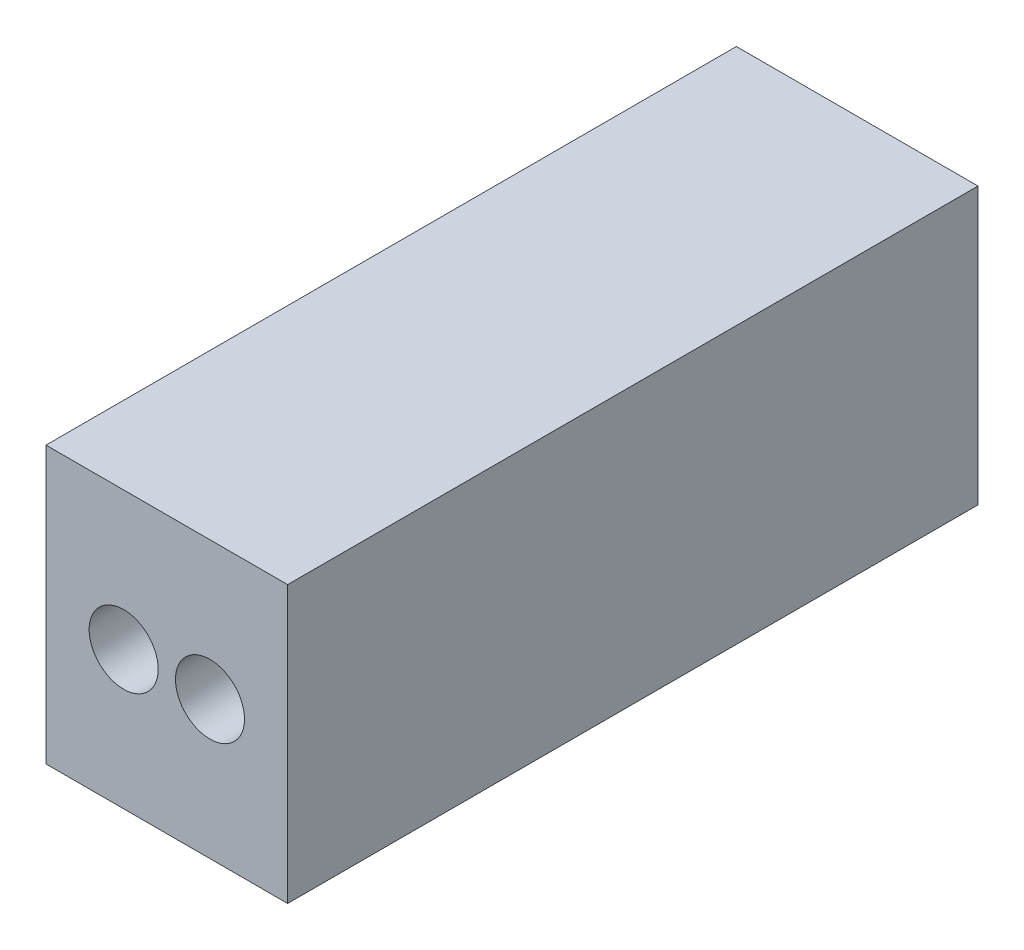
SolidWorks part; units mm, degrees
ref_plane "Front Plane" through (0, 0, 0) normal (0, 0, 1) x (1, 0, 0)
ref_plane "Top Plane" through (0, 0, 0) normal (0, 1, 0) x (1, 0, 0)
ref_plane "Right Plane" through (0, 0, 0) normal (1, 0, 0) x (0, 0, -1)
sketch "Sketch2" plane through (0, 0, 0) normal (0, 0, 1) x (1, 0, 0)
  line L1 (0, 0) -> (3.5, 0)
  line L2 (0, 0) -> (0, 4)
  line L3 (0, 4) -> (3.5, 4)
  line L4 (3.5, 0) -> (3.5, 4)
  dimension "D1" = 3.5
  dimension "D2" = 4
extrude "Boss-Extrude1" add sketch "Sketch2" along normal blind 10
sketch "Sketch3" plane through (0, 0, 10) normal (0, 0, 1) x (1, 0, 0)
  line L0 (0, 2) -> (3.5, 2) construction
  line L1 (0, 4) -> (0, 0) construction
  line L2 (3.5, 0) -> (3.5, 4) construction
  line L3 (0, 2) -> (3.5, 2) construction
  line L4 (3.5, 4) -> (0, 4) construction
  line L5 (0, 0) -> (3.5, 0) construction
  line L6 (1.125, 4) -> (1.125, 0) construction
  circle A0 centre (1.125, 2) radius 0.5
  circle A1 centre (2.375, 2) radius 0.5
  circle A21 centre (24.875, 2) radius 0.5 [skipped]
  circle A22 centre (23.625, 2) radius 0.5 [skipped]
  circle A23 centre (22.375, 2) radius 0.5 [skipped]
  circle A24 centre (21.125, 2) radius 0.5 [skipped]
  circle A25 centre (19.875, 2) radius 0.5 [skipped]
  circle A26 centre (18.625, 2) radius 0.5 [skipped]
  circle A27 centre (17.375, 2) radius 0.5 [skipped]
  circle A28 centre (16.125, 2) radius 0.5 [skipped]
  circle A29 centre (14.875, 2) radius 0.5 [skipped]
  circle A30 centre (13.625, 2) radius 0.5 [skipped]
  circle A31 centre (12.375, 2) radius 0.5 [skipped]
  circle A32 centre (11.125, 2) radius 0.5 [skipped]
  circle A33 centre (9.875, 2) radius 0.5 [skipped]
  circle A34 centre (7.375, 2) radius 0.5 [skipped]
  circle A35 centre (8.625, 2) radius 0.5 [skipped]
  circle A36 centre (3.625, 2) radius 0.5 [skipped]
  circle A37 centre (4.875, 2) radius 0.5 [skipped]
  circle A38 centre (6.125, 2) radius 0.5 [skipped]
  dimension "D1" = 1
  dimension "D2" = 2
  dimension "D3" = 1.125
  dimension "D5" = 1.25
  dimension "D4" = 20
extrude "Cut-Extrude1" cut sketch "Sketch3" against normal blind 5
sketch "Sketch4" plane through (0, 0, 10) normal (0, 0, 1) x (1, 0, 0)
  point P0 (1.125, 2)
  point P1 (2.375, 2)
  point P9 (0, 0)
  point P11 (0, 0)
  point P13 (0, 0)
  point P15 (0, 0)
  point P17 (0, 0)
  point P27 (0, 0)
  point P37 (0, 0)
